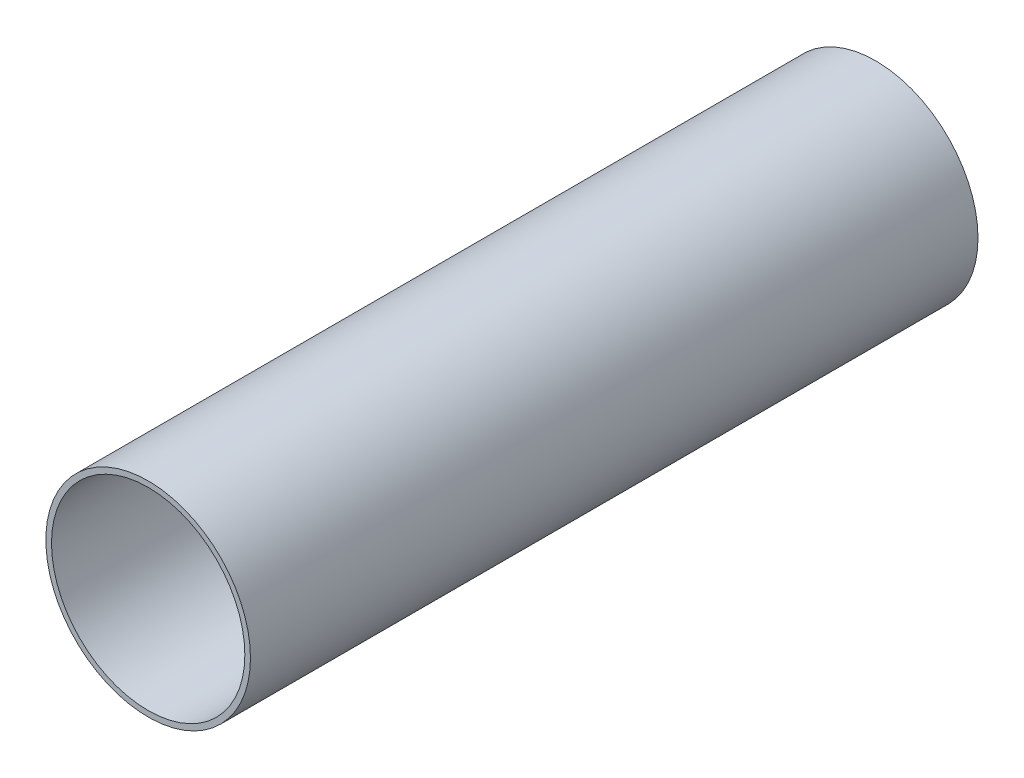
SolidWorks part; units mm, degrees
ref_plane "Front Plane" through (0, 0, 0) normal (0, 0, 1) x (1, 0, 0)
ref_plane "Top Plane" through (0, 0, 0) normal (0, 1, 0) x (1, 0, 0)
ref_plane "Right Plane" through (0, 0, 0) normal (1, 0, 0) x (0, 0, -1)
sketch "Sketch1" plane through (0, 0, 0) normal (0, 0, 1) x (1, 0, 0)
  circle A0 centre (0, 0) radius 28.575
  circle A1 centre (0, 0) radius 27.0002
  dimension "D1" = 54.0004
  dimension "D2" = 57.15
extrude "Boss-Extrude1" add sketch "Sketch1" along normal mid plane 203.2
equation "\"AIRFRAME_OD\"= 3.091in"
equation "\"AIRFRAME_ID\"= 3.00in"
equation "\"FLAT_T\"= 0.125in"
equation "\"NOSE_EXP_L\"= 3.5in"
equation "\"NOSE_SHOULDER_L\"= 5in"
equation "\"MAIN_L\"= 30in"
equation "\"RECO_COUP_L\"= 6in"
equation "\"RECO_SWITCH_L\"= 1.5in"
equation "\"DROGUE_L\"= 14in"
equation "\"ATS_FORE_COUP_L\"= 4in"
equation "\"ATS_AFT_COUP_L\"= 2.5in"
equation "\"LOWER_L\"= 16in"
equation "\"FIN_N\"= 4"
equation "\"CR_AFT_X\"= 0.5in"
equation "\"CR_FORE_X\"= 6in"
equation "\"D1@Sketch1\"=\"MOTOR_ID\""
equation "\"D2@Sketch1\"=\"MOTOR_OD\""
equation "\"D1@Boss-Extrude1\"=\"MOTOR_L\""
equation "\"FIN_ROOT\"= 5in"
equation "\"FIN_X\"= 0.75in"
equation "\"MOTOR_OD\"= 2.25in"
equation "\"MOTOR_ID\"= 2.126in"
equation "\"COUPLER_OD\"= 2.998in"
equation "\"COUPLER_ID\"= 2.875in"
equation "\"RECO_ROD_X\"= 1.5in"
equation "\"ATS_ROD_X\"= 2in"
equation "\"MOTOR_L\"= 8in"
